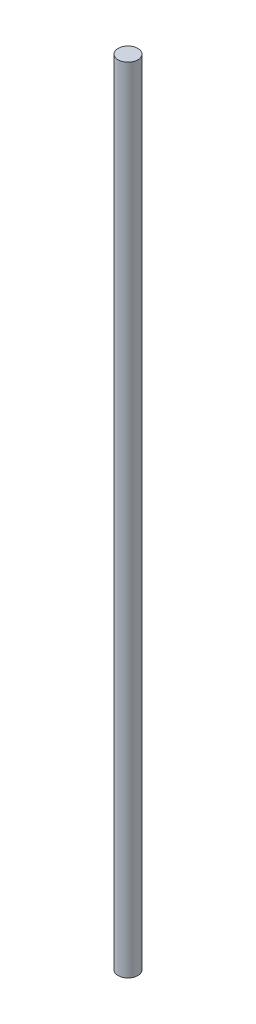
SolidWorks part; units mm, degrees
ref_plane "Front" through (0, 0, 0) normal (0, 0, 1) x (1, 0, 0)
ref_plane "Top" through (0, 0, 0) normal (0, 1, 0) x (1, 0, 0)
ref_plane "Right" through (0, 0, 0) normal (1, 0, 0) x (0, 0, -1)
sketch "Sketch1" plane through (0, 0, 0) normal (0, 1, 0) x (1, 0, 0)
  circle A0 centre (0, 0) radius 1.5
  dimension "D1" = 3
extrude "Boss-Extrude1" add sketch "Sketch1" along normal blind 120
